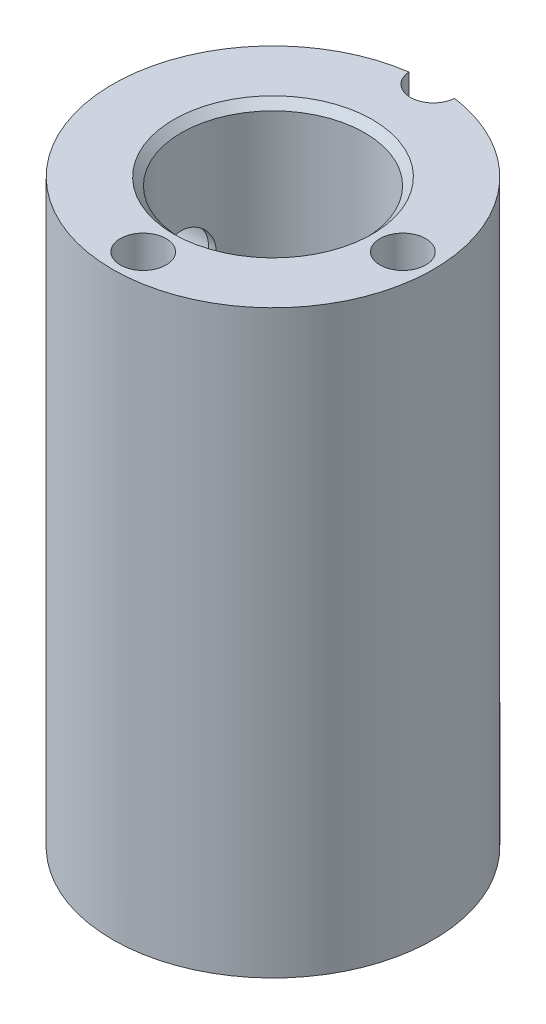
SolidWorks part; units mm, degrees
material "Chrome Stainless Steel"
ref_plane "Front Plane" through (0, 0, 0) normal (0, 0, 1) x (1, 0, 0)
ref_plane "Top Plane" through (0, 0, 0) normal (0, 1, 0) x (1, 0, 0)
ref_plane "Right Plane" through (0, 0, 0) normal (1, 0, 0) x (0, 0, -1)
sketch "Sketch1" plane through (0, 0, 0) normal (0, 1, 0) x (1, 0, 0)
  circle A0 centre (0, 0) radius 10.5
  dimension "D1" = 21
extrude "Boss-Extrude1" add sketch "Sketch1" along normal blind 38
sketch "Sketch2" plane through (0, 38, 0) normal (0, 1, 0) x (1, 0, 0)
  circle A0 centre (0, 0) radius 6
  dimension "D1" = 12
extrude "Cut-Extrude1" cut sketch "Sketch2" against normal through all
ref_plane "Plane1" through (-10.5, 0, 0) normal (-1, 0, 0) x (0, 0, 1)
sketch "Sketch5" plane through (-10.5, 0, 0) normal (-1, 0, 0) x (0, 0, 1)
  line L0 (0, 30.0697) -> (0, 9.6952) construction
  line L1 (-3.5264, 30) -> (4.3883, 30) construction
  line L2 (6, 38) -> (-6, 38) construction
  dimension "D1" = 8
hole_wizard "Ø3.9 (3.9) Diameter Hole1" positions "Sketch6" profile "Sketch7" hole size "Ø3.9" standard "ANSI Metric"
sketch "Sketch6" plane through (-10.5, 0, 0) normal (-1, 0, 0) x (0, 0, 1)
  line L0 (0, 30.0697) -> (0, 9.6952) construction
  line L1 (-3.5264, 30) -> (4.3883, 30) construction
  point P0 (0, 30)
sketch "Sketch7" plane through (-10.5, 30, 0) normal (0, 1, 0) x (0, 0, 1)
  line L0 (0, 0) -> (0, 4.5)
  line L1 (0, 4.5) -> (1.95, 4.5)
  line L2 (1.95, 4.5) -> (1.95, 0)
  line L5 (1.95, 0) -> (0, 0)
  line L11 (0, -6.35) -> (0, 107.95) construction
  dimension "Thru Hole Dia." = 3.9
  dimension "Thru Hole Depth" = 4.5
hole_wizard "Ø5.0mm Dowel Hole1" positions "Sketch8" profile "Sketch9" hole size "Ø5.0" standard "ANSI Metric"
sketch "Sketch8" plane through (-10.5, 0, 0) normal (-1, 0, 0) x (0, 0, 1)
  point P0 (0, 30)
sketch "Sketch9" plane through (-10.5, 30, 0) normal (0, 1, 0) x (0, 0, 1)
  line L0 (0, 0) -> (0, 5.5022)
  line L1 (0, 5.5022) -> (2.5, 4)
  line L2 (2.5, 4) -> (2.5, 0)
  line L5 (2.5, 0) -> (0, 0)
  line L10 (0, 5.5022) -> (-2.5, 4) construction
  line L11 (0, -6.35) -> (0, 107.95) construction
  dimension "Hole Dia." = 5
  dimension "Hole Depth" = 4
  dimension "Drill Angle" = 118
ref_plane "Plane2" through (0, 18.5, 0) normal (0, -1, 0) x (-1, 0, 0)
mirror "Mirror1" about plane through (0, 18.5, 0) normal (0, -1, 0) of "Ø5.0mm Dowel Hole1", "Ø3.9 (3.9) Diameter Hole1"
sketch "Sketch11" plane through (0, 38, 0) normal (0, 1, 0) x (1, 0, 0)
  line L0 (7.4572, 0) -> (9.7179, 0) construction
  line L1 (0, -7.467) -> (0, -9.2772) construction
  circle A0 centre (0, 0) radius 8.5 construction
  dimension "D1" = 17
hole_wizard "Ø3.0mm Dowel Hole1" positions "Sketch12" profile "Sketch13" hole size "Ø3.0" standard "ANSI Metric"
sketch "Sketch12" plane through (0, 38, 0) normal (0, 1, 0) x (1, 0, 0)
  line L0 (7.4572, 0) -> (9.7179, 0) construction
  line L1 (0, -7.467) -> (0, -9.2772) construction
  circle A0 centre (0, 0) radius 8.5 construction
  point P0 (8.5, 0)
  point P6 (0, -8.5)
sketch "Sketch13" plane through (8.5, 38, 0) normal (1, 0, 0) x (0, 0, 1)
  line L0 (0, 0) -> (0, 6.9013)
  line L1 (0, 6.9013) -> (1.5, 6)
  line L2 (1.5, 6) -> (1.5, 0)
  line L5 (1.5, 0) -> (0, 0)
  line L10 (0, 6.9013) -> (-1.5, 6) construction
  line L11 (0, -6.35) -> (0, 107.95) construction
  dimension "Hole Dia." = 3
  dimension "Hole Depth" = 6
  dimension "Drill Angle" = 118
chamfer "Chamfer1" distance 0.5 angle 45 1 edges at (0, 38, 6)
hole_wizard "Ø3.0mm Dowel Hole2" positions "Sketch14" profile "Sketch15" hole size "Ø3.0" standard "ANSI Metric"
sketch "Sketch14" plane through (0, 38, 0) normal (0, 1, 0) x (1, 0, 0)
  point P0 (0, 10.5)
sketch "Sketch15" plane through (0, 38, -10.5) normal (1, 0, 0) x (0, 0, 1)
  line L0 (0, 0) -> (0, 8.9013)
  line L1 (0, 8.9013) -> (1.5, 8)
  line L2 (1.5, 8) -> (1.5, 0)
  line L5 (1.5, 0) -> (0, 0)
  line L10 (0, 8.9013) -> (-1.5, 8) construction
  line L11 (0, -6.35) -> (0, 107.95) construction
  dimension "Hole Dia." = 3
  dimension "Hole Depth" = 8
  dimension "Drill Angle" = 118
